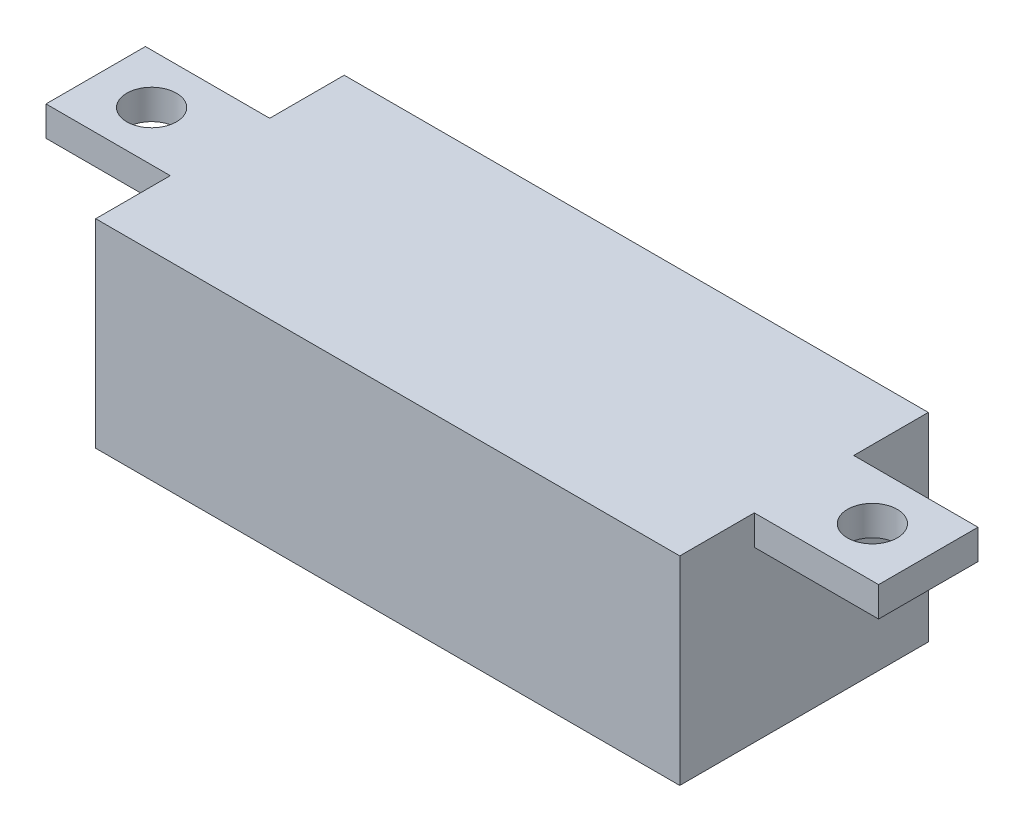
SolidWorks part; units mm, degrees
ref_plane "Front Plane" through (0, 0, 0) normal (0, 0, 1) x (1, 0, 0)
ref_plane "Top Plane" through (0, 0, 0) normal (0, 1, 0) x (1, 0, 0)
ref_plane "Right Plane" through (0, 0, 0) normal (1, 0, 0) x (0, 0, -1)
sketch "Sketch1" plane through (0, 0, 0) normal (0, 1, 0) x (1, 0, 0)
  line L1 (11.75, -5) -> (-11.75, -5)
  line L2 (11.75, -5) -> (11.75, 5)
  line L3 (11.75, 5) -> (-11.75, 5)
  line L4 (-11.75, -5) -> (-11.75, 5)
  line L5 (11.75, -5) -> (-11.75, 5) construction
  line L6 (11.75, 5) -> (-11.75, -5) construction
  point P0 (0, 0)
  dimension "D1" = 23.5
  dimension "D2" = 10
extrude "Boss-Extrude1" add sketch "Sketch1" along normal blind 8
sketch "Sketch2" plane through (0, 8, 0) normal (0, 1, 0) x (1, 0, 0)
  line L0 (-15.0432, 0) -> (16.7953, 0) construction
  line L1 (0, 8.1707) -> (0, -9.028) construction
  line L2 (11.75, -5) -> (11.75, 5) construction
  line L3 (16.75, -2) -> (6.75, -2)
  line L4 (16.75, -2) -> (16.75, 2)
  line L5 (16.75, 2) -> (6.75, 2)
  line L6 (6.75, -2) -> (6.75, 2)
  line L7 (16.75, -2) -> (6.75, 2) construction
  line L8 (16.75, 2) -> (6.75, -2) construction
  line L9 (-16.75, 2) -> (-6.75, -2) construction
  line L10 (-16.75, -2) -> (-6.75, 2) construction
  line L11 (15.0432, 0) -> (-16.7953, 0) construction
  line L12 (-6.75, -2) -> (-6.75, 2)
  line L13 (-16.75, 2) -> (-6.75, 2)
  line L14 (-16.75, -2) -> (-16.75, 2)
  line L15 (-16.75, -2) -> (-6.75, -2)
  circle A0 centre (14.5, 0) radius 1
  circle A1 centre (-14.5, 0) radius 1
  point P5 (11.75, 0)
  point P18 (-11.75, 0)
  dimension "D3" = 2
  dimension "D1" = 4
  dimension "D2" = 5
  dimension "D4" = 29
extrude "Boss-Extrude2" add sketch "Sketch2" against normal blind 1.2
